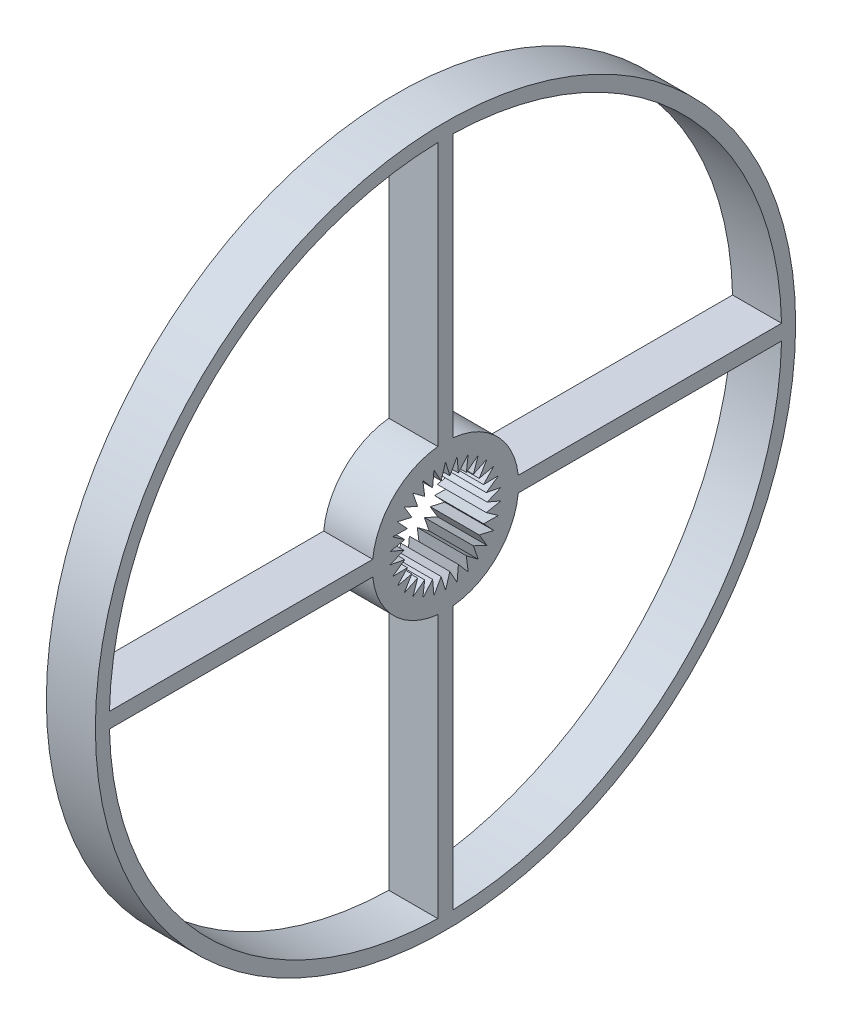
SolidWorks part; units mm, degrees
ref_plane "Front Plane" through (0, 0, 0) normal (0, 0, 1) x (1, 0, 0)
ref_plane "Top Plane" through (0, 0, 0) normal (0, 1, 0) x (1, 0, 0)
ref_plane "Right Plane" through (0, 0, 0) normal (1, 0, 0) x (0, 0, -1)
sketch "Sketch3" plane through (0, 0, 0) normal (1, 0, 0) x (0, 0, -1)
  line L0 (0, 0) -> (0, 7.95) construction
  line L1 (0, 0) -> (0.831, 7.9064) construction
  line L2 (0, 0) -> (-0.831, 7.9064) construction
  line L3 (0, 7.95) -> (-0.6219, 5.9174)
  line L4 (0, 7.95) -> (0.6219, 5.9174)
  line L5 (1.6529, 7.7763) -> (0.6219, 5.9174)
  line L6 (1.6529, 7.7763) -> (1.8387, 5.6588)
  line L7 (3.2336, 7.2627) -> (1.8387, 5.6588)
  line L8 (3.2336, 7.2627) -> (2.975, 5.1529)
  line L9 (4.6729, 6.4317) -> (2.975, 5.1529)
  line L10 (4.6729, 6.4317) -> (3.9813, 4.4217)
  line L11 (5.908, 5.3196) -> (3.9813, 4.4217)
  line L12 (5.908, 5.3196) -> (4.8137, 3.4973)
  line L13 (6.8849, 3.975) -> (4.8137, 3.4973)
  line L14 (6.8849, 3.975) -> (5.4356, 2.4201)
  line L15 (7.5609, 2.4567) -> (5.4356, 2.4201)
  line L16 (7.5609, 2.4567) -> (5.82, 1.2371)
  line L17 (7.9064, 0.831) -> (5.82, 1.2371)
  line L18 (7.9064, 0.831) -> (5.95, 0)
  line L19 (7.9064, -0.831) -> (5.95, 0)
  line L20 (7.9064, -0.831) -> (5.82, -1.2371)
  line L21 (7.5609, -2.4567) -> (5.82, -1.2371)
  line L22 (7.5609, -2.4567) -> (5.4356, -2.4201)
  line L23 (6.8849, -3.975) -> (5.4356, -2.4201)
  line L24 (6.8849, -3.975) -> (4.8137, -3.4973)
  line L25 (5.908, -5.3196) -> (4.8137, -3.4973)
  line L26 (5.908, -5.3196) -> (3.9813, -4.4217)
  line L27 (4.6729, -6.4317) -> (3.9813, -4.4217)
  line L28 (4.6729, -6.4317) -> (2.975, -5.1529)
  line L29 (3.2336, -7.2627) -> (2.975, -5.1529)
  line L30 (3.2336, -7.2627) -> (1.8387, -5.6588)
  line L31 (1.6529, -7.7763) -> (1.8387, -5.6588)
  line L32 (1.6529, -7.7763) -> (0.6219, -5.9174)
  line L33 (0, -7.95) -> (0.6219, -5.9174)
  line L34 (0, -7.95) -> (-0.6219, -5.9174)
  line L35 (-1.6529, -7.7763) -> (-0.6219, -5.9174)
  line L36 (-1.6529, -7.7763) -> (-1.8387, -5.6588)
  line L37 (-3.2336, -7.2627) -> (-1.8387, -5.6588)
  line L38 (-3.2336, -7.2627) -> (-2.975, -5.1529)
  line L39 (-4.6729, -6.4317) -> (-2.975, -5.1529)
  line L40 (-4.6729, -6.4317) -> (-3.9813, -4.4217)
  line L41 (-5.908, -5.3196) -> (-3.9813, -4.4217)
  line L42 (-5.908, -5.3196) -> (-4.8137, -3.4973)
  line L43 (-6.8849, -3.975) -> (-4.8137, -3.4973)
  line L44 (-6.8849, -3.975) -> (-5.4356, -2.4201)
  line L45 (-7.5609, -2.4567) -> (-5.4356, -2.4201)
  line L46 (-7.5609, -2.4567) -> (-5.82, -1.2371)
  line L47 (-7.9064, -0.831) -> (-5.82, -1.2371)
  line L48 (-7.9064, -0.831) -> (-5.95, 0)
  line L49 (-7.9064, 0.831) -> (-5.95, 0)
  line L50 (-7.9064, 0.831) -> (-5.82, 1.2371)
  line L51 (-7.5609, 2.4567) -> (-5.82, 1.2371)
  line L52 (-7.5609, 2.4567) -> (-5.4356, 2.4201)
  line L53 (-6.8849, 3.975) -> (-5.4356, 2.4201)
  line L54 (-6.8849, 3.975) -> (-4.8137, 3.4973)
  line L55 (-5.908, 5.3196) -> (-4.8137, 3.4973)
  line L56 (-5.908, 5.3196) -> (-3.9813, 4.4217)
  line L57 (-4.6729, 6.4317) -> (-3.9813, 4.4217)
  line L58 (-4.6729, 6.4317) -> (-2.975, 5.1529)
  line L59 (-3.2336, 7.2627) -> (-2.975, 5.1529)
  line L60 (-3.2336, 7.2627) -> (-1.8387, 5.6588)
  line L61 (-1.6529, 7.7763) -> (-1.8387, 5.6588)
  line L62 (-1.6529, 7.7763) -> (-0.6219, 5.9174)
  line L63 (-1.0923, 10.3928) -> (-1.0923, 47.9876)
  line L64 (1.0923, 10.3928) -> (1.0923, 47.9876)
  line L65 (10.3928, 1.0923) -> (47.9876, 1.0923)
  line L66 (10.3928, -1.0923) -> (47.9876, -1.0923)
  line L67 (1.0923, -10.3928) -> (1.0923, -47.9876)
  line L68 (-1.0923, -10.3928) -> (-1.0923, -47.9876)
  line L69 (-10.3928, -1.0923) -> (-47.9876, -1.0923)
  line L70 (-10.3928, 1.0923) -> (-47.9876, 1.0923)
  circle A0 centre (0, 0) radius 7.95 construction
  arc A1 (-1.0923, 10.3928) -> (-10.3928, 1.0923) centre (0, 0) ccw
  circle A2 centre (0, 0) radius 50
  arc A3 (-1.0923, 47.9876) -> (-47.9876, 1.0923) centre (0, 0) ccw
  circle A4 centre (0, 0) radius 5.95 construction
  circle A5 centre (0, 0) radius 48 construction
  circle A6 centre (0, 0) radius 10.45 construction
  arc A7 (10.3928, 1.0923) -> (1.0923, 10.3928) centre (0, 0) ccw
  arc A8 (47.9876, 1.0923) -> (1.0923, 47.9876) centre (0, 0) ccw
  arc A9 (-47.9876, -1.0923) -> (-1.0923, -47.9876) centre (0, 0) ccw
  arc A10 (-10.3928, -1.0923) -> (-1.0923, -10.3928) centre (0, 0) ccw
  arc A11 (1.0923, -47.9876) -> (47.9876, -1.0923) centre (0, 0) ccw
  arc A12 (1.0923, -10.3928) -> (10.3928, -1.0923) centre (0, 0) ccw
  point P79 (0, 0)
  point P105 (0, 0)
  dimension "D1" = 15.9
  dimension "D3" = 100
  dimension "D4" = 6
  dimension "D5" = 2
  dimension "D2" = 2.5
  dimension "D6" = 30
  dimension "D7" = 4
extrude "Boss-Extrude2" add sketch "Sketch3" along normal blind 7
